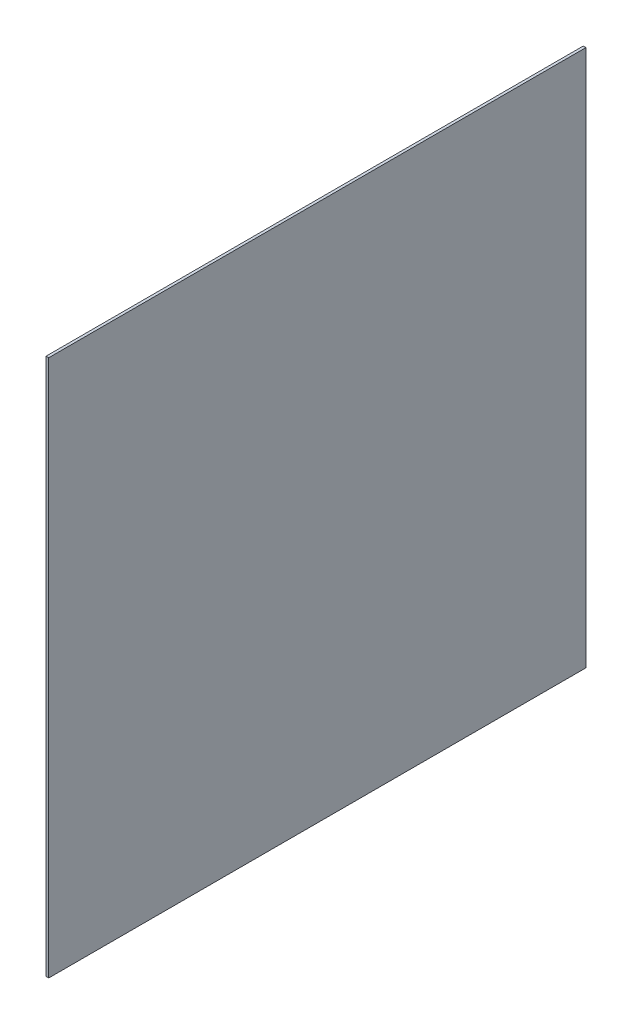
SolidWorks part; units mm, degrees
ref_plane "前视基准面" through (0, 0, 0) normal (0, 0, 1) x (1, 0, 0)
ref_plane "上视基准面" through (0, 0, 0) normal (0, 1, 0) x (1, 0, 0)
ref_plane "右视基准面" through (0, 0, 0) normal (1, 0, 0) x (0, 0, -1)
sketch "草图1" plane through (0, 0, 0) normal (1, 0, 0) x (0, 0, -1)
  line L0 (-100, 100) -> (100, 100)
  line L1 (-100, 100) -> (-100, -100)
  line L2 (100, 100) -> (100, -100)
  line L3 (-100, -100) -> (100, -100)
  line L4 (-100, 100) -> (100, -100) construction
  line L5 (100, 100) -> (-100, -100) construction
  point P1 (0, 0)
extrude "凸台-拉伸1" add sketch "草图1" along normal blind 1
